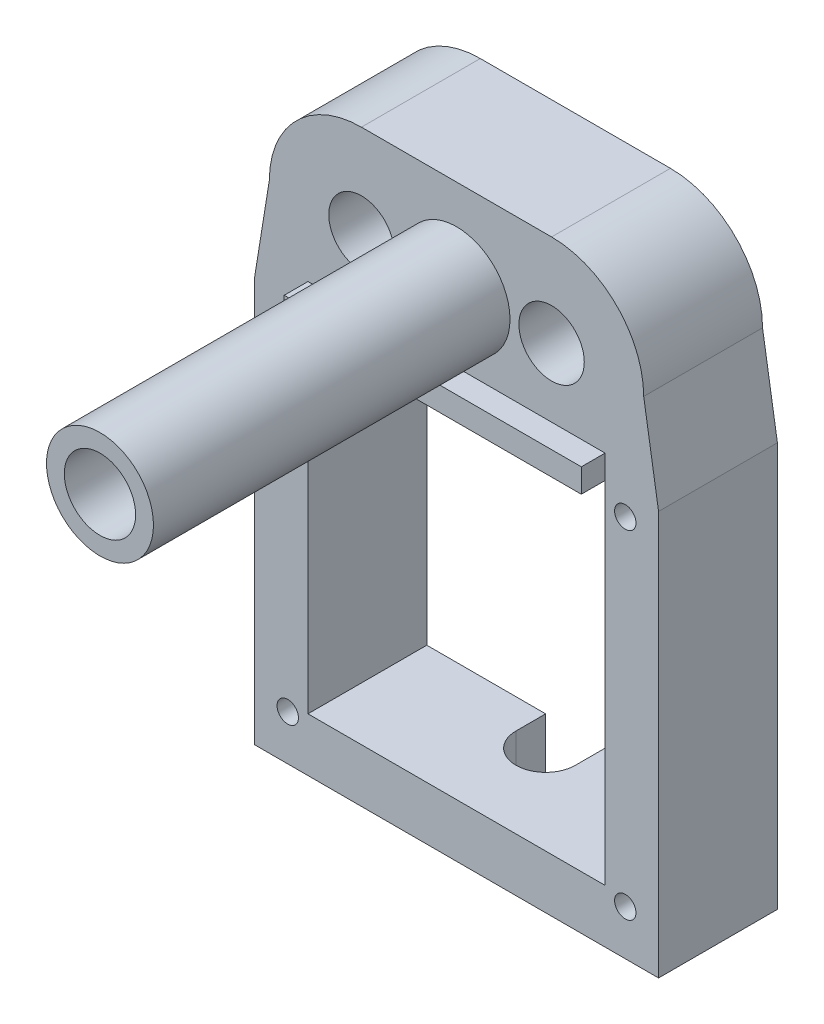
SolidWorks part; units mm, degrees
ref_plane "前视基准面" through (0, 0, 0) normal (0, 0, 1) x (1, 0, 0)
ref_plane "上视基准面" through (0, 0, 0) normal (0, 1, 0) x (1, 0, 0)
ref_plane "右视基准面" through (0, 0, 0) normal (1, 0, 0) x (0, 0, -1)
other "Configuration Table"
sketch "Sketch1" plane through (0, 0, 0) normal (0, 0, 1) x (1, 0, 0)
  line L0 (-8, 0) -> (8, 0) construction
  line L1 (-8, 7.75) -> (8, 7.75)
  line L2 (-8, -7.75) -> (8, -7.75)
  circle A0 centre (-8, 0) radius 2.75
  circle A1 centre (8, 0) radius 2.75
  circle A2 centre (-8, 0) radius 7.75
  circle A3 centre (8, 0) radius 7.75
  point P5 (0, 0)
  dimension "D2" = 5.5
  dimension "D3" = 5.5
  dimension "D1" = 16
  dimension "D4" = 5
extrude "Boss-Extrude1" add sketch "Sketch1" along normal blind 10
sketch "Sketch2" plane through (0, 0, 10) normal (0, 0, 1) x (1, 0, 0)
  circle A0 centre (0, 0) radius 3
  dimension "D1" = 6
extrude "Cut-Extrude1" cut sketch "Sketch2" against normal blind 15
sketch "Sketch3" plane through (0, 0, 10) normal (0, 0, 1) x (1, 0, 0)
  circle A0 centre (0, 0) radius 3
  circle A1 centre (0, 0) radius 4.5
  circle A3 centre (0, 0) radius 3 construction
  dimension "D1" = 1.5
extrude "Boss-Extrude2" add sketch "Sketch3" along normal blind 30
sketch "Sketch5" plane through (0, 0, 0) normal (0, 0, 1) x (1, 0, 0)
  line L0 (-15.75, 0) -> (-17, -7.75)
  line L1 (-17, -7.75) -> (17, -7.75)
  line L2 (17, -7.75) -> (15.75, 0)
  line L3 (-8, -7.75) -> (8, -7.75)
  line L4 (-12.5, -12.25) -> (-12.5, -37.25)
  line L5 (-17, -7.75) -> (17, -7.75)
  line L6 (-17, -7.75) -> (-17, -41.75)
  line L7 (-17, -41.75) -> (17, -41.75)
  line L8 (17, -7.75) -> (17, -41.75)
  line L9 (-12.5, -37.25) -> (12.5, -37.25)
  line L10 (12.5, -12.25) -> (12.5, -37.25)
  line L11 (-12.5, -12.25) -> (12.5, -12.25)
  line L12 (-12.5, -12.25) -> (-12.5, -7.75)
  line L13 (12.5, -12.25) -> (12.5, -7.75)
  arc A0 (-8, 7.75) -> (-8, -7.75) centre (-8, 0) ccw construction
  arc A1 (8, -7.75) -> (8, 7.75) centre (8, 0) ccw construction
  circle A2 centre (-8, 0) radius 7.75
  circle A3 centre (8, 0) radius 7.75
  point P20 (0, -7.75)
  dimension "D1" = 34
  dimension "D2" = 34
  dimension "D3" = 4.5
extrude "Boss-Extrude4" add sketch "Sketch5" along normal blind 10 contours L13 L10 L9 L4 L12 L1 L6 L7 L8 L5 | A2 L0 L1 L5 | A3 L1 L5 L2
sketch "Sketch6" plane through (0, -41.75, 0) normal (0, -1, 0) x (1, 0, 0)
  line L0 (-17, 0) -> (17, 0) construction
  line L1 (-2.5, 2.5) -> (-2.5, 0)
  line L2 (-2.5, 0) -> (2.5, 0)
  line L3 (2.5, 0) -> (2.5, 2.5)
  circle A0 centre (0, 2.5) radius 2.5
  point P8 (-6.8306, 2.5)
  line M4 (-17, 0) -> (17, 0)
  dimension "D1" = 5
extrude "Cut-Extrude2" cut sketch "Sketch6" against normal blind 10 contours A0 | A0 L1 M4 | A0 L2 L3
sketch "Sketch7" plane through (0, 0, 10) normal (0, 0, 1) x (1, 0, 0)
  line L0 (12.5, -37.25) -> (12.5, -7.75) construction
  line L1 (-12.5, -7.75) -> (12.5, -7.75)
  line L2 (-12.5, -7.75) -> (-12.5, -5.75)
  line L3 (-12.5, -5.75) -> (12.5, -5.75)
  line L4 (12.5, -7.75) -> (12.5, -5.75)
  dimension "D1" = 2
extrude "Boss-Extrude6" add sketch "Sketch7" along normal blind 2
sketch "Sketch8" plane through (0, 0, 10) normal (0, 0, 1) x (1, 0, 0)
  line L0 (-12.5, -7.75) -> (12.5, -7.75) construction
  line L1 (-16, -7.75) -> (16, -7.75) construction
  line L2 (-16, -7.75) -> (-16, -39.75) construction
  line L3 (-16, -39.75) -> (16, -39.75) construction
  line L4 (16, -7.75) -> (16, -39.75) construction
  line L5 (0, -7.75) -> (0, -39.75) construction
  line L6 (-16, -23.75) -> (16, -23.75) construction
  circle A0 centre (-14.2, -9.55) radius 0.9
  circle A1 centre (14.2, -9.55) radius 0.9
  circle A2 centre (14.2, -37.95) radius 0.9
  circle A3 centre (-14.2, -37.95) radius 0.9
  point P6 (0, -7.75)
  dimension "D5" = 1.8
  dimension "D1" = 32
  dimension "D2" = 32
  dimension "D3" = 1.8
  dimension "D4" = 1.8
extrude "Cut-Extrude3" cut sketch "Sketch8" against normal blind 19
